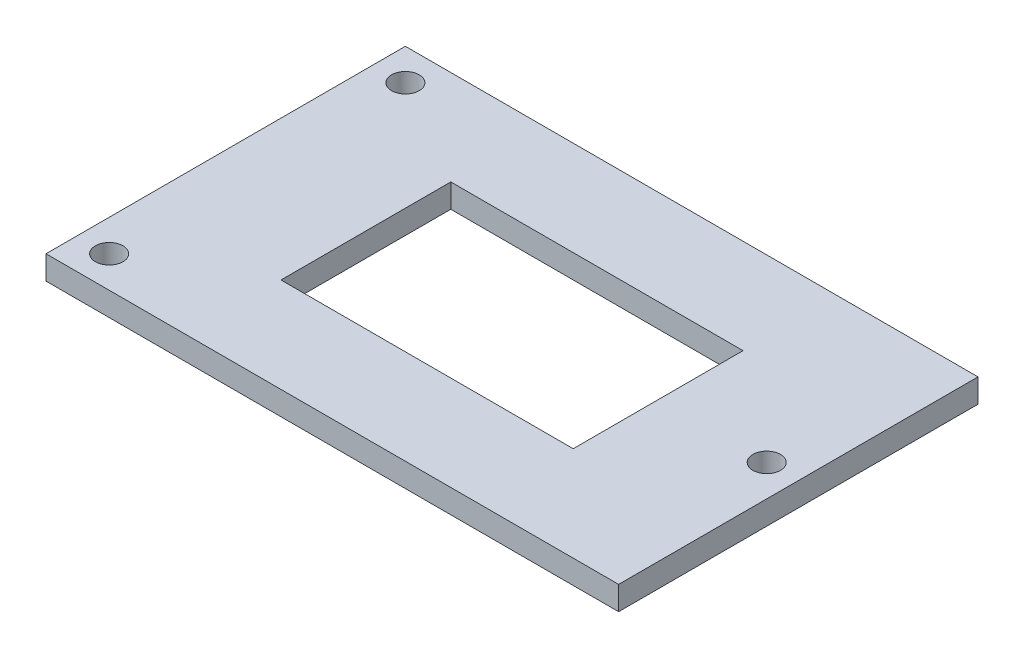
SolidWorks part; units mm, degrees
material "ABS"
ref_plane "Front Plane" through (0, 0, 0) normal (0, 0, 1) x (1, 0, 0)
ref_plane "Top Plane" through (0, 0, 0) normal (0, 1, 0) x (1, 0, 0)
ref_plane "Right Plane" through (0, 0, 0) normal (1, 0, 0) x (0, 0, -1)
sketch "Sketch1" plane through (0, 0, 0) normal (0, 1, 0) x (1, 0, 0)
  line L1 (0, 0) -> (72.5, 0)
  line L2 (0, 0) -> (0, 45.5)
  line L3 (0, 45.5) -> (72.5, 45.5)
  line L4 (72.5, 0) -> (72.5, 45.5)
  line L5 (17.75, 12) -> (54.75, 12)
  line L6 (17.75, 12) -> (17.75, 33.5)
  line L7 (17.75, 33.5) -> (54.75, 33.5)
  line L8 (54.75, 12) -> (54.75, 33.5)
  circle A0 centre (68.5, 22.75) radius 1.75
  circle A1 centre (4, 41.5) radius 1.75
  circle A2 centre (4, 4) radius 1.75
  dimension "D7" = 3.5
  dimension "D8" = 3.5
  dimension "D9" = 3.5
  dimension "D1" = 72.5
  dimension "D2" = 45.5
  dimension "D3" = 37
  dimension "D4" = 21.5
  dimension "D5" = 12
  dimension "D6" = 17.75
  dimension "D10" = 4
  dimension "D11" = 4
  dimension "D12" = 4
  dimension "D13" = 4
  dimension "D14" = 22.75
  dimension "D15" = 4
extrude "Boss-Extrude1" add sketch "Sketch1" along normal blind 3
